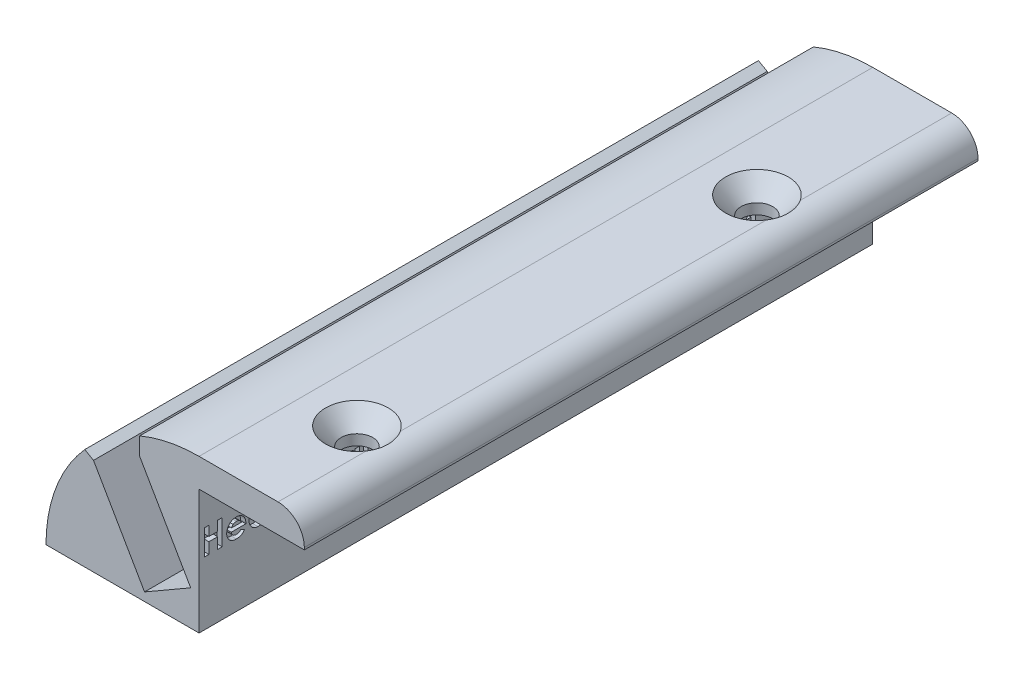
SolidWorks part; units mm, degrees
ref_plane "Front Plane" through (0, 0, 0) normal (0, 0, 1) x (1, 0, 0)
ref_plane "Top Plane" through (0, 0, 0) normal (0, 1, 0) x (1, 0, 0)
ref_plane "Right Plane" through (0, 0, 0) normal (1, 0, 0) x (0, 0, -1)
sketch "Sketch1" plane through (0, 0, 0) normal (0, 0, 1) x (1, 0, 0)
  line L0 (-43.8658, 7.3279) -> (-25.4, 7.3279)
  line L1 (-127, 7.3279) -> (127, 7.3279) construction
  line L2 (-25.4, 7.3279) -> (-25.4, 21.9837)
  line L3 (-25.4, 22.3647) -> (-14.6818, 22.3647)
  line L4 (-25.4, 21.9837) -> (228.6, 21.9837) construction
  line L5 (-25.4, 22.3647) -> (-25.4, 21.9837)
  line L6 (-38.1345, 19.0062) -> (-41.9445, 21.2059)
  line L7 (-41.9445, 21.2059) -> (-32.5693, 26.6187)
  line L8 (-32.5693, 26.6187) -> (-32.5693, 22.2193)
  line L9 (-25.4, 7.3279) -> (-34.6329, 23.3198) construction
  line L14 (-25.4, 25.7937) -> (-15.875, 25.7937)
  line L15 (-12.7, 22.6187) -> (-12.7, 22.3647)
  line L16 (-12.7, 22.3647) -> (-14.6818, 22.3647)
  line L18 (-38.1345, 19.0062) -> (-31.975, 8.3377)
  line L19 (-31.975, 8.3377) -> (-26.4098, 11.5508)
  line L20 (-26.4098, 11.5508) -> (-32.5693, 22.2193)
  line L21 (-32.5693, 22.2193) -> (-38.1345, 19.0062)
  line L22 (-38.1345, 19.0062) -> (-31.975, 8.3377)
  line L23 (-31.975, 8.3377) -> (-26.4098, 11.5508)
  line L24 (-26.4098, 11.5508) -> (-32.5693, 22.2193)
  line L25 (-32.5693, 22.2193) -> (-38.1345, 19.0062)
  circle A0 centre (-25.4, 7.3279) radius 18.4658
  arc A1 (-15.875, 25.7937) -> (-12.7, 22.6187) centre (-15.875, 22.6187) cw
  point P3 (-25.4, 25.7937)
  point P7 (-25.4, 21.9837)
  point P20 (-27.0497, 10.1852)
  dimension "D8" = 3.175
  dimension "D1" = 3.81
  dimension "D2" = 0.381
  dimension "D3" = 60
  dimension "D4" = 0.1905
  dimension "D5" = 30
  dimension "D6" = 30
  dimension "D7" = 3.81
  dimension "D9" = 12.7
extrude "Boss-Extrude1" add sketch "Sketch1" along normal mid plane 81.28 contours L0 L9 L23 L22 L6 A0 | L9 L2 L5 L3 A0 L8 L24 L23 | A1 L14 A0 L16 L15
ref_plane "Plane1" through (0, 0, 27.94) normal (0, 0, 1) x (1, 0, 0)
sketch "Sketch4" plane through (0, 0, 27.94) normal (0, 0, 1) x (1, 0, 0)
  line L0 (-17.145, 22.3647) -> (-17.145, 23.6347)
  line L1 (-25.4, 22.3647) -> (-12.7, 22.3647) construction
  line L2 (-17.145, 23.6347) -> (-13.833, 27.4447)
  line L3 (-13.833, 27.4447) -> (-19.05, 27.4447)
  line L4 (-19.05, 27.4447) -> (-19.05, 22.3647)
  line L5 (-19.05, 22.3647) -> (-17.145, 22.3647)
  dimension "D1" = 1.905
  dimension "D2" = 1.27
  dimension "D3" = 41
  dimension "D4" = 5.08
  dimension "D5" = 6.35
revolve "Cut-Revolve1" cut sketch "Sketch4" angle 360 about L4
pattern_linear "LPattern1" count 2 spacing 48.26 along (0, 0, -1) of "Cut-Revolve1"
sketch "Sketch5" plane through (-25.4, 0, 0) normal (1, 0, 0) x (0, 0, -1)
  line L0 (-69.1647, 14.9479) -> (67.826, 14.9479) construction
  line L1 (-40.64, 7.3279) -> (40.64, 7.3279) construction
  text T0 "<b>Headboard Ceiling LED Mount V1 3.2in</b>" font "Century Gothic" height 3.048
  point P3 (0, 14.9479)
  dimension "D1" = 7.62
extrude "Cut-Extrude2" cut sketch "Sketch5" against normal blind 0.635
